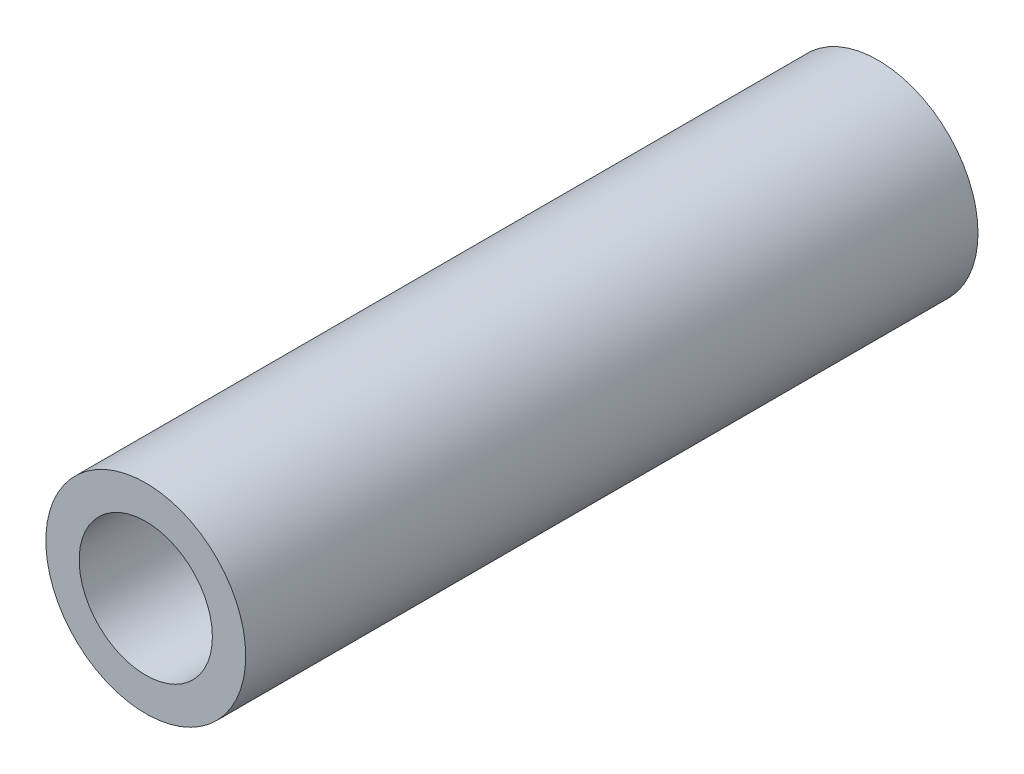
SolidWorks part; units mm, degrees
ref_plane "Front Plane" through (0, 0, 0) normal (0, 0, 1) x (1, 0, 0)
ref_plane "Top Plane" through (0, 0, 0) normal (0, 1, 0) x (1, 0, 0)
ref_plane "Right Plane" through (0, 0, 0) normal (1, 0, 0) x (0, 0, -1)
sketch "Sketch1" plane through (0, 0, 0) normal (0, 0, 1) x (1, 0, 0)
  circle A0 centre (0, 0) radius 2.3813 construction
  dimension "Diameter" = 4.7625
sketch "Sketch2" plane through (0, 0, 0) normal (1, 0, 0) x (0, 0, -1)
  line L0 (-8.7249, 0) -> (8.7249, 0) construction
  line L1 (-8.7249, 2.3813) -> (8.7249, 2.3813) construction
  line L3 (0, 2.3813) -> (0, -2.3813) construction
  point P0 (-6.1849, 0)
  point P3 (0, 0)
  point P4 (6.1849, 0)
  point P9 (0, 2.3813)
  dimension "D1" = 2.54
  dimension "D2" = 2.54
  dimension "Length" = 17.4498
sketch "Sketch3" plane through (0, 0, 0) normal (0, 0, 1) x (1, 0, 0)
  circle A0 centre (0, 0) radius 2.3813 construction
  circle A1 centre (0, 0) radius 2.3813
extrude "Boss-Extrude1" add sketch "Sketch3" against normal up to vertex (8.7249 mm away) from vertex at 8.7249 starting at point (0, 0, 8.7249)
sketch "Sketch4" plane through (0, 0, 8.7249) normal (0, 0, 1) x (1, 0, 0)
  circle A0 centre (0, 0) radius 1.5875
  dimension "D1" = 3.175
extrude "Cut-Extrude1" cut sketch "Sketch4" against normal up to next
equation "\"D2@Sketch2\"=\"D1@Sketch2\""
